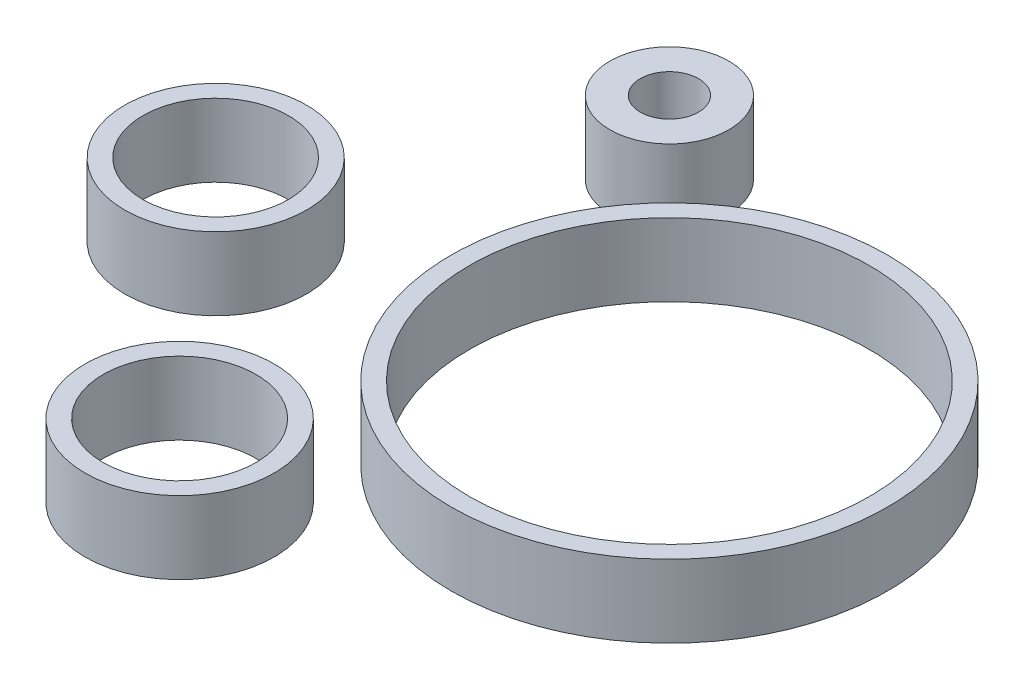
SolidWorks part; units mm, degrees
ref_plane "前视基准面" through (0, 0, 0) normal (0, 0, 1) x (1, 0, 0)
ref_plane "上视基准面" through (0, 0, 0) normal (0, 1, 0) x (1, 0, 0)
ref_plane "右视基准面" through (0, 0, 0) normal (1, 0, 0) x (0, 0, -1)
sketch "草图1" plane through (0, 0, 0) normal (0, 1, 0) x (1, 0, 0)
  circle A0 centre (-12.9842, -10.3092) radius 15
  circle A1 centre (-29.9842, 6.6908) radius 2
  circle A2 centre (-41.8744, -12.6009) radius 5
  circle A3 centre (-41.8744, -12.6009) radius 6.25
  circle A4 centre (-27.5852, -29.3676) radius 5.25
  circle A5 centre (-29.9842, 6.6908) radius 4.0912
  circle A6 centre (-27.5852, -29.3676) radius 6.5
  circle A9 centre (-12.9842, -10.3092) radius 13.75
  dimension "D3" = 30
  dimension "D4" = 12.5
  dimension "D5" = 10.5
  dimension "D6" = 13
  dimension "D7" = 4
  dimension "D1" = 27.5
  dimension "D2" = 10
extrude "凸台-拉伸1" add sketch "草图1" along normal blind 5
